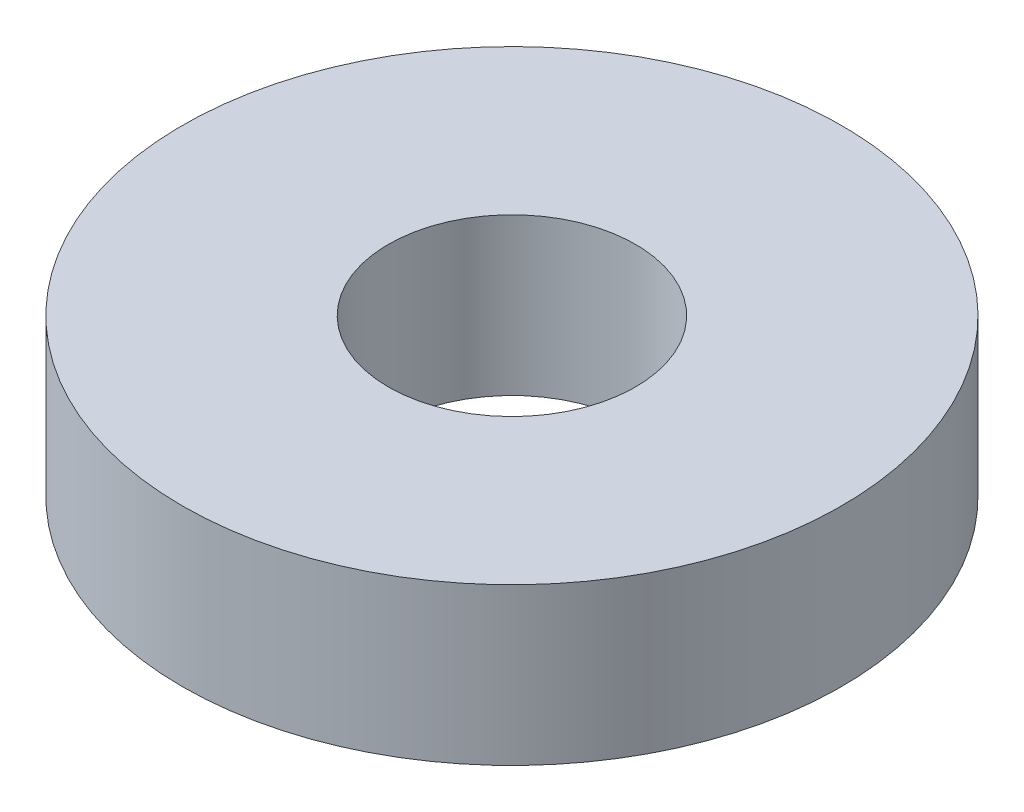
SolidWorks part; units mm, degrees
ref_plane "Front Plane" through (0, 0, 0) normal (0, 0, 1) x (1, 0, 0)
ref_plane "Top Plane" through (0, 0, 0) normal (0, 1, 0) x (1, 0, 0)
ref_plane "Right Plane" through (0, 0, 0) normal (1, 0, 0) x (0, 0, -1)
sketch "Sketch1" plane through (0, 0, 0) normal (0, 1, 0) x (1, 0, 0)
  circle A0 centre (0, 0) radius 4
  circle A1 centre (0, 0) radius 1.5
  dimension "D1" = 8
  dimension "D2" = 3
extrude "Boss-Extrude1" add sketch "Sketch1" along normal blind 1.9
